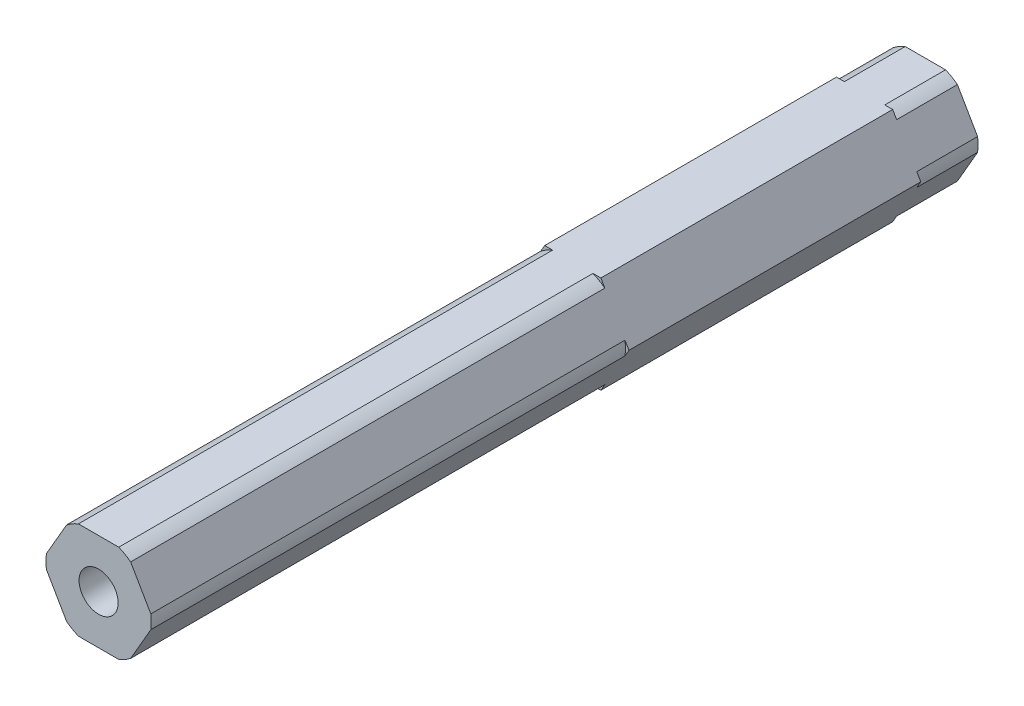
SolidWorks part; units mm, degrees
material "6061-T6 (SS)"
ref_plane "Front Plane" through (0, 0, 0) normal (0, 0, 1) x (1, 0, 0)
ref_plane "Top Plane" through (0, 0, 0) normal (0, 1, 0) x (1, 0, 0)
ref_plane "Right Plane" through (0, 0, 0) normal (1, 0, 0) x (0, 0, -1)
sketch "Sketch1" plane through (0, 0, 0) normal (0, 0, 1) x (1, 0, 0)
  line L1 (-7.3323, 0) -> (-3.6662, -6.35)
  line L2 (-3.6662, -6.35) -> (3.6662, -6.35)
  line L3 (3.6662, -6.35) -> (7.3323, 0)
  line L4 (7.3323, 0) -> (3.6662, 6.35)
  line L5 (3.6662, 6.35) -> (-3.6662, 6.35)
  line L6 (-3.6662, 6.35) -> (-7.3323, 0)
  circle A0 centre (0, 0) radius 6.35 construction
  dimension "D1" = 12.7
extrude "Boss-Extrude1" add sketch "Sketch1" along normal mid plane 38.1
sketch "Sketch2" plane through (0, 0, 19.05) normal (0, 0, 1) x (1, 0, 0)
  line L0 (7.3323, 0) -> (3.6662, 6.35) construction
  line L1 (3.6662, -6.35) -> (7.3323, 0) construction
  line L2 (-3.6662, -6.35) -> (3.6662, -6.35) construction
  line L3 (-7.3323, 0) -> (-3.6662, -6.35) construction
  line L4 (-3.6662, 6.35) -> (-7.3323, 0) construction
  line L5 (3.6662, 6.35) -> (-3.6662, 6.35) construction
  line L6 (6.8168, 0.893) -> (4.1818, 5.457)
  line L7 (4.1818, -5.457) -> (6.8168, -0.893)
  line L8 (-2.635, -6.35) -> (2.635, -6.35)
  line L9 (-6.8168, -0.893) -> (-4.1818, -5.457)
  line L10 (-4.1818, 5.457) -> (-6.8168, 0.893)
  line L11 (2.635, 6.35) -> (-2.635, 6.35)
  arc A0 (-2.635, 6.35) -> (-4.1818, 5.457) centre (0, 0) ccw
  arc A1 (4.1818, 5.457) -> (2.635, 6.35) centre (0, 0) ccw
  arc A2 (6.8168, -0.893) -> (6.8168, 0.893) centre (0, 0) ccw
  arc A3 (2.635, -6.35) -> (4.1818, -5.457) centre (0, 0) ccw
  arc A4 (-4.1818, -5.457) -> (-2.635, -6.35) centre (0, 0) ccw
  arc A5 (-6.8168, 0.893) -> (-6.8168, -0.893) centre (0, 0) ccw
  dimension "D1" = 13.75
extrude "Boss-Extrude2" add sketch "Sketch2" along normal blind 7.9375
mirror "Mirror1" about plane through (0, 0, 0) normal (0, 0, 1) of "Boss-Extrude2"
sketch "Sketch3" plane through (0, 0, 26.9875) normal (0, 0, 1) x (1, 0, 0)
  line L0 (6.8168, 0.893) -> (4.1818, 5.457) construction
  line L1 (4.1818, -5.457) -> (6.8168, -0.893) construction
  line L2 (-2.635, -6.35) -> (2.635, -6.35) construction
  line L3 (-6.8168, -0.893) -> (-4.1818, -5.457) construction
  line L4 (-4.1818, 5.457) -> (-6.8168, 0.893) construction
  line L5 (2.635, 6.35) -> (-2.635, 6.35) construction
  line L6 (6.8168, 0.893) -> (4.1818, 5.457)
  line L7 (4.1818, -5.457) -> (6.8168, -0.893)
  line L8 (-2.635, -6.35) -> (2.635, -6.35)
  line L9 (-6.8168, -0.893) -> (-4.1818, -5.457)
  line L10 (-4.1818, 5.457) -> (-6.8168, 0.893)
  line L11 (2.635, 6.35) -> (-2.635, 6.35)
  arc A0 (4.1818, 5.457) -> (2.635, 6.35) centre (0, 0) ccw construction
  arc A1 (6.8168, -0.893) -> (6.8168, 0.893) centre (0, 0) ccw construction
  arc A2 (2.635, -6.35) -> (4.1818, -5.457) centre (0, 0) ccw construction
  arc A3 (-4.1818, -5.457) -> (-2.635, -6.35) centre (0, 0) ccw construction
  arc A4 (-6.8168, 0.893) -> (-6.8168, -0.893) centre (0, 0) ccw construction
  arc A5 (-2.635, 6.35) -> (-4.1818, 5.457) centre (0, 0) ccw construction
  arc A6 (4.1818, 5.457) -> (2.635, 6.35) centre (0, 0) ccw
  arc A7 (6.8168, -0.893) -> (6.8168, 0.893) centre (0, 0) ccw
  arc A8 (2.635, -6.35) -> (4.1818, -5.457) centre (0, 0) ccw
  arc A9 (-4.1818, -5.457) -> (-2.635, -6.35) centre (0, 0) ccw
  arc A10 (-6.8168, 0.893) -> (-6.8168, -0.893) centre (0, 0) ccw
  arc A11 (-2.635, 6.35) -> (-4.1818, 5.457) centre (0, 0) ccw
extrude "Boss-Extrude3" add sketch "Sketch3" along normal blind 53.975
sketch "Sketch6" plane through (0, 0, -26.9875) normal (0, 0, -1) x (-1, 0, 0)
  circle A0 centre (0, 0) radius 3.175
  dimension "D1" = 6.35
extrude "Cut-Extrude1" cut sketch "Sketch6" against normal blind 11.811
hole_wizard "#10-32 Tapped Hole1" positions "Sketch7" profile "Sketch9" tap size "#10-32" standard "ANSI Inch"
sketch "Sketch7" plane through (0, 0, -15.1765) normal (0, 0, -1) x (-1, 0, 0)
  point P0 (0, 0)
sketch "Sketch9" plane through (0, 0, -15.1765) normal (1, 0, 0) x (0, 1, 0)
  line L0 (0, 0) -> (0, 13.2529)
  line L1 (0, 13.2529) -> (2.0193, 12.0396)
  line L2 (2.0193, 12.0396) -> (2.0193, 0)
  line L5 (2.0193, 0) -> (0, 0)
  line L10 (0, 13.2529) -> (-2.0193, 12.0396) construction
  line L11 (0, -6.35) -> (0, 107.95) construction
  dimension "Tap Drill Dia." = 4.0386
  dimension "Tap Drill Depth" = 12.0396
  dimension "Drill Angle" = 118
cosmetic thread "Hole Thread1" parameters "D1"=9.652, "D2"=4.826
hole_wizard "1/4-20 Tapped Hole1" positions "Sketch10" profile "Sketch12" tap size "1/4-20" standard "ANSI Inch"
sketch "Sketch10" plane through (0, 0, 80.9625) normal (0, 0, 1) x (1, 0, 0)
  point P0 (0, 0)
sketch "Sketch12" plane through (0, 0, 80.9625) normal (1, 0, 0) x (0, -1, 0)
  line L0 (0, 0) -> (0, 20.5838)
  line L1 (0, 20.5838) -> (2.5527, 19.05)
  line L2 (2.5527, 19.05) -> (2.5527, 0)
  line L5 (2.5527, 0) -> (0, 0)
  line L10 (0, 20.5838) -> (-2.5527, 19.05) construction
  line L11 (0, -6.35) -> (0, 107.95) construction
  dimension "Tap Drill Dia." = 5.1054
  dimension "Tap Drill Depth" = 19.05
  dimension "Drill Angle" = 118
cosmetic thread "Hole Thread2" parameters "D1"=8.128, "D2"=6.35
